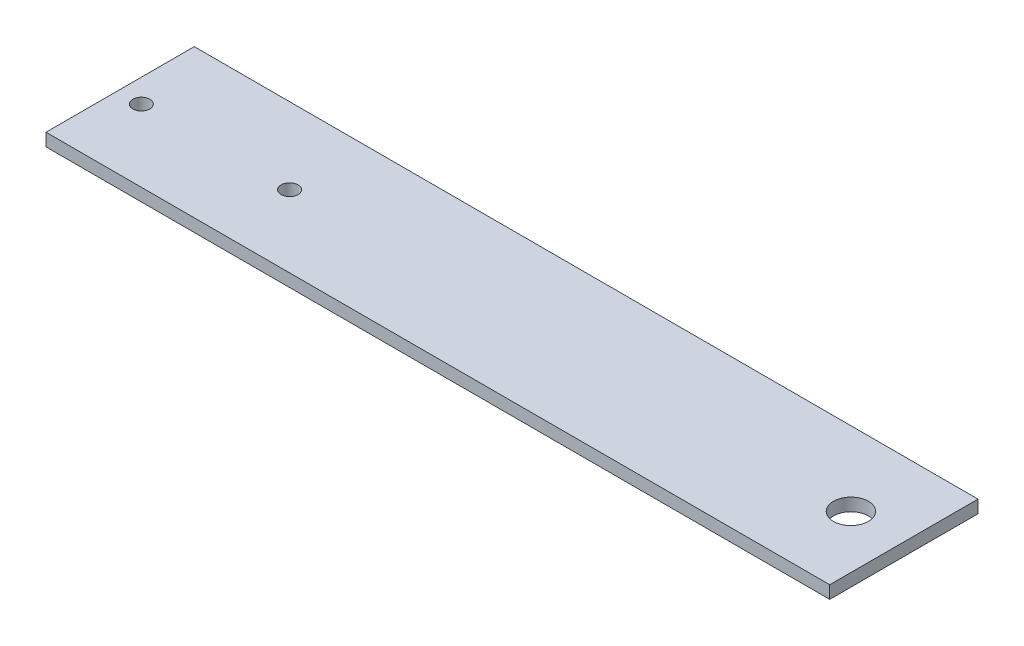
SolidWorks part; units mm, degrees
ref_plane "Front Plane" through (0, 0, 0) normal (0, 0, 1) x (1, 0, 0)
ref_plane "Top Plane" through (0, 0, 0) normal (0, 1, 0) x (1, 0, 0)
ref_plane "Right Plane" through (0, 0, 0) normal (1, 0, 0) x (0, 0, -1)
sketch "Sketch1" plane through (0, 0, 0) normal (0, 1, 0) x (1, 0, 0)
  line L1 (-92.5, 17.5) -> (92.5, 17.5)
  line L2 (-92.5, 17.5) -> (-92.5, -17.5)
  line L3 (-92.5, -17.5) -> (92.5, -17.5)
  line L4 (92.5, 17.5) -> (92.5, -17.5)
  line L5 (-92.5, 17.5) -> (92.5, -17.5) construction
  line L6 (-92.5, -17.5) -> (92.5, 17.5) construction
  circle A0 centre (-10.6801, 3.3392) radius 4.5
  circle A1 centre (-10.6585, -3.6607) radius 14
  circle A2 centre (-28.1585, -4.7634) radius 2
  circle A3 centre (6.8415, -4.7634) radius 2
  circle A4 centre (80, 0) radius 4.125
  point P0 (0, 0)
  point P17 (92.5, 0)
  dimension "D3" = 12.5
  dimension "D4" = 4
  dimension "D5" = 4
  dimension "D6" = 8.25
  dimension "D1" = 35
  dimension "D2" = 185
  dimension "D7" = 8.1025
  dimension "D8" = 8.1025
  dimension "D9" = 17.5
extrude "Boss-Extrude1" add sketch "Sketch1" along normal blind 3 contours A1 L3 L4 L1 L2 A4 A3 A2 | L3 A1 A0 | A2 | A3
sketch "Sketch2" plane through (0, 3, 0) normal (0, 1, 0) x (1, 0, 0)
  line L0 (-92.5, 17.5) -> (-92.5, -17.5) construction
  line L1 (-92.5, -17.5) -> (92.5, -17.5) construction
  line L2 (-69.5, 6.5) -> (-69.5, -6.7467) construction
  circle A0 centre (-69.5, 6.5) radius 3
  circle A1 centre (-69.5, 6.5) radius 15 construction
  circle A2 centre (-27, 6.5) radius 27.5 construction
  circle A3 centre (-87, -0.5) radius 2
  circle A4 centre (-52, -0.5) radius 2
  dimension "D1" = 6
  dimension "D3" = 24
  dimension "D4" = 7
  dimension "D2" = 23
  dimension "D5" = 17.5
extrude "Cut-Extrude1" cut sketch "Sketch2" against normal through all contours A3 | A4
